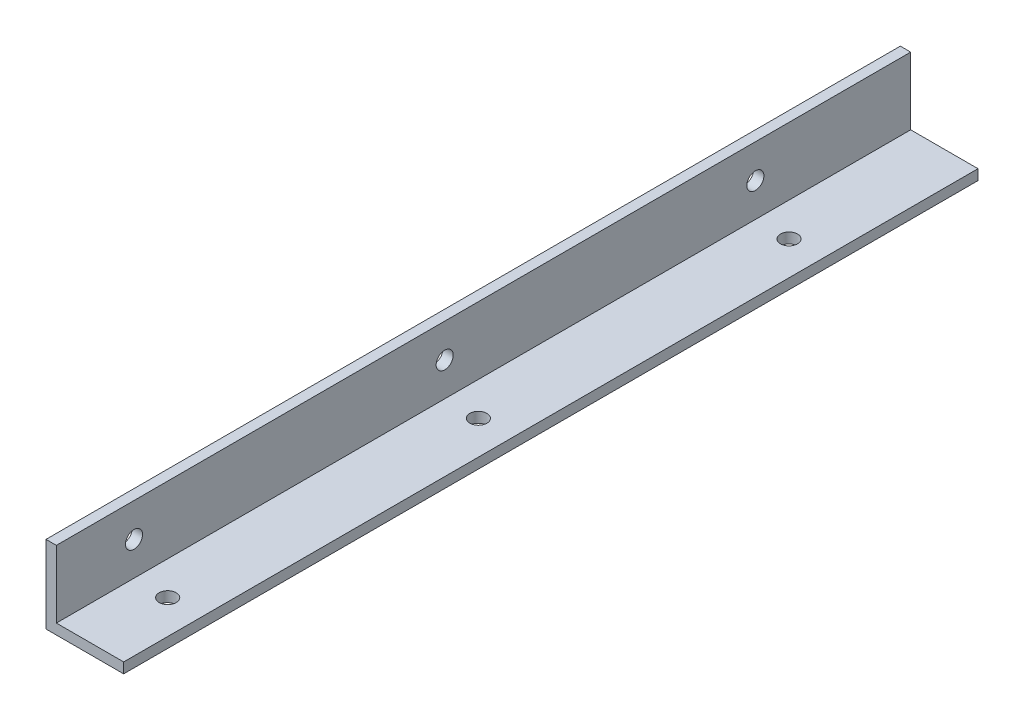
SolidWorks part; units mm, degrees
ref_plane "正面" through (0, 0, 0) normal (0, 0, 1) x (1, 0, 0)
ref_plane "平面" through (0, 0, 0) normal (0, 1, 0) x (1, 0, 0)
ref_plane "右側面" through (0, 0, 0) normal (1, 0, 0) x (0, 0, -1)
sketch "ｽｹｯﾁ1" plane through (0, 0, 0) normal (0, 0, 1) x (1, 0, 0)
  line L0 (0, 0) -> (0, 15)
  line L1 (0, 15) -> (2, 15)
  line L2 (2, 15) -> (2, 2)
  line L3 (2, 2) -> (15, 2)
  line L4 (15, 2) -> (15, 0)
  line L5 (15, 0) -> (0, 0)
  dimension "D1" = 15
  dimension "D2" = 15
  dimension "D3" = 2
  dimension "D4" = 2
  dimension "D5" = 13
extrude "ﾎﾞｽ - 押し出し1" add sketch "ｽｹｯﾁ1" along normal blind 150
ref_plane "平面1" through (15, 2, 150) normal (0, 0, -1) x (-1, 0, 0)
sketch "ｽｹｯﾁ5" plane through (0, 2, 0) normal (0, 1, 0) x (1, 0, 0)
  line L0 (8.5, 0) -> (8.5, -15)
  line L1 (15, 0) -> (2, 0) construction
  line L2 (8.5, -150) -> (8.5, -135)
  line L3 (56.25, -150) -> (-26.25, -150) construction
  line L4 (8.5, -150) -> (8.5, -75)
  circle A0 centre (8.5, -135) radius 2.2
  circle A1 centre (8.5, -15) radius 2.2
  circle A2 centre (8.5, -75) radius 2.2
  dimension "D4" = 4.4
  dimension "D5" = 4.4
  dimension "D6" = 4.4
  dimension "D1" = 15
  dimension "D2" = 15
  dimension "D3" = 75
sketch "ｽｹｯﾁ6" plane through (2, 0, 0) normal (1, 0, 0) x (0, 0, -1)
  line L0 (0, 8.5) -> (-15, 8.5)
  line L1 (0, 2) -> (0, 15) construction
  line L2 (-150, 8.5) -> (-135, 8.5)
  line L3 (-150, -39.25) -> (-150, 43.25) construction
  line L4 (-150, 8.5) -> (-75, 8.5)
  circle A0 centre (-135, 8.5) radius 2.2
  circle A1 centre (-75, 8.5) radius 2.2
  circle A2 centre (-15, 8.5) radius 2.2
  dimension "D4" = 4.4
  dimension "D5" = 4.4
  dimension "D6" = 4.4
  dimension "D1" = 15
  dimension "D2" = 15
  dimension "D3" = 75
sketch "ｽｹｯﾁ7" plane through (0, 0, 0) normal (0, 0, -1) x (-1, 0, 0)
  line L0 (-15, 2) -> (-2, 2)
  line L1 (-2, 2) -> (-2, 15)
  line L2 (-2, 15) -> (0, 15)
  line L3 (0, 15) -> (0, 0)
  line L4 (0, 0) -> (-15, 0)
  line L5 (0, 0) -> (-15, 0) construction
  line L6 (-15, 0) -> (-15, 2)
extrude "ﾎﾞｽ - 押し出し2" add sketch "ｽｹｯﾁ7" along normal blind 15
hole_wizard "M4x0.7 ねじ穴1" positions "3Dｽｹｯﾁ1" profile "ｽｹｯﾁ8" tap size "M4x0.7" standard "JIS"
sketch3d "3Dｽｹｯﾁ1"
  point P0 (8.5, 2, 15)
  point P3 (8.5, 2, 75)
  point P6 (8.5, 2, 135)
  point P9 (2, 8.5, 135)
  point P12 (2, 8.5, 75)
  point P15 (2, 8.5, 15)
sketch "ｽｹｯﾁ8" plane through (8.5, 2, 15) normal (1, 0, 0) x (0, 0, 1)
  line L0 (0, 0) -> (0, 12.4914)
  line L1 (0, 12.4914) -> (1.65, 11.5)
  line L2 (1.65, 11.5) -> (1.65, 0)
  line L5 (1.65, 0) -> (0, 0)
  line L10 (0, 12.4914) -> (-1.65, 11.5) construction
  line L11 (0, -6.35) -> (0, 107.95) construction
  dimension "ねじ下穴ﾄﾞﾘﾙ直径" = 3.3
  dimension "ねじ下穴ﾄﾞﾘﾙの深さ" = 11.5
  dimension "ﾄﾞﾘﾙ角度" = 118
cosmetic thread "穴のねじ山1" parameters "D1"=2, "D2"=4
cosmetic thread "穴のねじ山2" parameters "D1"=2, "D2"=4
cosmetic thread "穴のねじ山3" parameters "D1"=2, "D2"=4
cosmetic thread "穴のねじ山4" parameters "D1"=2, "D2"=4
cosmetic thread "穴のねじ山5" parameters "D1"=2, "D2"=4
cosmetic thread "穴のねじ山6" parameters "D1"=2, "D2"=4
